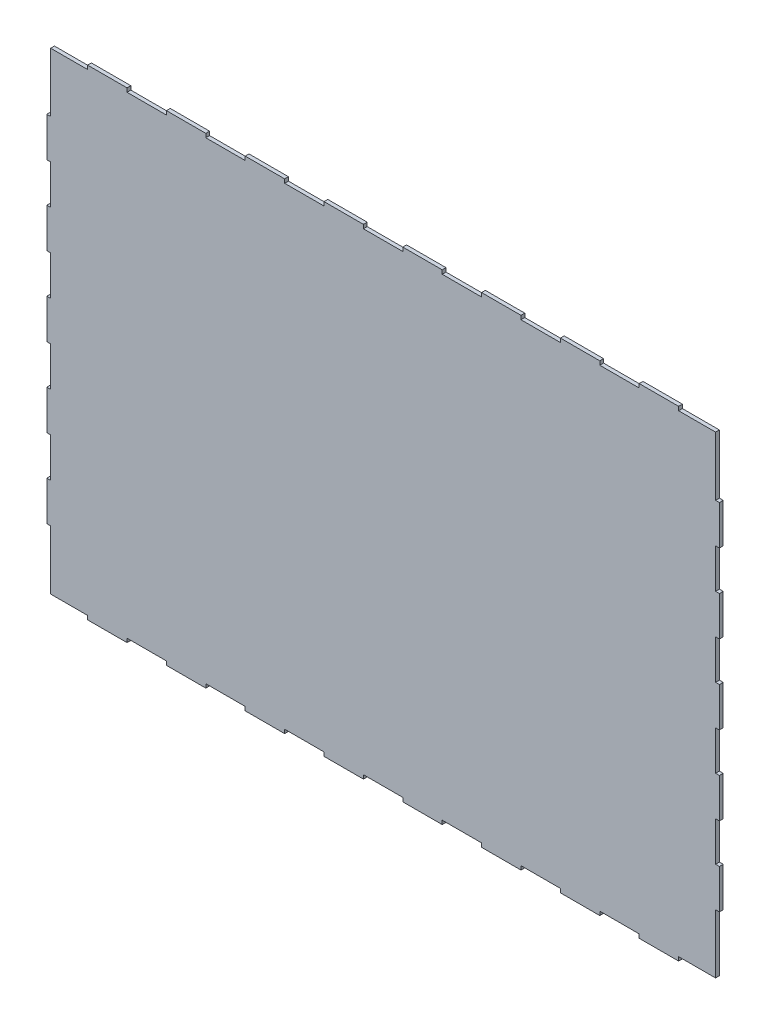
SolidWorks part; units mm, degrees
ref_plane "Front Plane" through (0, 0, 0) normal (0, 0, 1) x (1, 0, 0)
ref_plane "Top Plane" through (0, 0, 0) normal (0, 1, 0) x (1, 0, 0)
ref_plane "Right Plane" through (0, 0, 0) normal (1, 0, 0) x (0, 0, -1)
sketch "Sketch1" plane through (0, 0, 0) normal (0, 0, 1) x (1, 0, 0)
  line B0 (-1.4841, 0.1451) -> (487.4659, 0.1451)
  line B1 (487.4659, 0.1451) -> (487.4659, -50.6549)
  line B2 (487.4659, -50.6549) -> (1008.1659, -50.6549)
  line B3 (1008.1659, -50.6549) -> (1008.1659, 0.1451)
  line B4 (1008.1659, 0.1451) -> (1528.8659, 0.1451)
  line B5 (1528.8659, 0.1451) -> (1528.8659, -50.6549)
  line B6 (1528.8659, -50.6549) -> (2049.5659, -50.6549)
  line B7 (2049.5659, -50.6549) -> (2049.5659, 0.1451)
  line B8 (2049.5659, 0.1451) -> (2570.2659, 0.1451)
  line B9 (2570.2659, 0.1451) -> (2570.2659, -50.6549)
  line B10 (2570.2659, -50.6549) -> (3090.9659, -50.6549)
  line B11 (3090.9659, -50.6549) -> (3090.9659, 0.1451)
  line B12 (3090.9659, 0.1451) -> (3611.6659, 0.1451)
  line B13 (3611.6659, 0.1451) -> (3611.6659, -50.6549)
  line B14 (3611.6659, -50.6549) -> (4132.3659, -50.6549)
  line B15 (4132.3659, -50.6549) -> (4132.3659, 0.1451)
  line B16 (4132.3659, 0.1451) -> (4653.0659, 0.1451)
  line B17 (4653.0659, 0.1451) -> (4653.0659, -50.6549)
  line B18 (4653.0659, -50.6549) -> (5173.7659, -50.6549)
  line B19 (5173.7659, -50.6549) -> (5173.7659, 0.1451)
  line B20 (5173.7659, 0.1451) -> (5694.4659, 0.1451)
  line B21 (5694.4659, 0.1451) -> (5694.4659, -50.6549)
  line B22 (5694.4659, -50.6549) -> (6215.1659, -50.6549)
  line B23 (6215.1659, -50.6549) -> (6215.1659, 0.1451)
  line B24 (6215.1659, 0.1451) -> (6735.8659, 0.1451)
  line B25 (6735.8659, 0.1451) -> (6735.8659, -50.6549)
  line B26 (6735.8659, -50.6549) -> (7256.5659, -50.6549)
  line B27 (7256.5659, -50.6549) -> (7256.5659, 0.1451)
  line B28 (7256.5659, 0.1451) -> (7777.2659, 0.1451)
  line B29 (7777.2659, 0.1451) -> (7777.2659, -50.6549)
  line B30 (7777.2659, -50.6549) -> (8297.9659, -50.6549)
  line B31 (8297.9659, -50.6549) -> (8297.9659, 0.1451)
  line B32 (8297.9659, 0.1451) -> (8786.9159, 0.1451)
  line B33 (8786.9159, 0.1451) -> (8786.9159, 781.1951)
  line B34 (8786.9159, 781.1951) -> (8837.7159, 781.1951)
  line B35 (8837.7159, 781.1951) -> (8837.7159, 1301.8951)
  line B36 (8837.7159, 1301.8951) -> (8786.9159, 1301.8951)
  line B37 (8786.9159, 1301.8951) -> (8786.9159, 1822.5951)
  line B38 (8786.9159, 1822.5951) -> (8837.7159, 1822.5951)
  line B39 (8837.7159, 1822.5951) -> (8837.7159, 2343.2951)
  line B40 (8837.7159, 2343.2951) -> (8786.9159, 2343.2951)
  line B41 (8786.9159, 2343.2951) -> (8786.9159, 2863.9951)
  line B42 (8786.9159, 2863.9951) -> (8837.7159, 2863.9951)
  line B43 (8837.7159, 2863.9951) -> (8837.7159, 3384.6951)
  line B44 (8837.7159, 3384.6951) -> (8786.9159, 3384.6951)
  line B45 (8786.9159, 3384.6951) -> (8786.9159, 3905.3951)
  line B46 (8786.9159, 3905.3951) -> (8837.7159, 3905.3951)
  line B47 (8837.7159, 3905.3951) -> (8837.7159, 4426.0951)
  line B48 (8837.7159, 4426.0951) -> (8786.9159, 4426.0951)
  line B49 (8786.9159, 4426.0951) -> (8786.9159, 4946.7951)
  line B50 (8786.9159, 4946.7951) -> (8837.7159, 4946.7951)
  line B51 (8837.7159, 4946.7951) -> (8837.7159, 5467.4951)
  line B52 (8837.7159, 5467.4951) -> (8786.9159, 5467.4951)
  line B53 (8786.9159, 5467.4951) -> (8786.9159, 5988.1951)
  line B54 (8786.9159, 5988.1951) -> (8786.9159, 6248.5451)
  line B55 (8786.9159, 6248.5451) -> (8297.9659, 6248.5451)
  line B56 (8297.9659, 6248.5451) -> (8297.9659, 6299.3451)
  line B57 (8297.9659, 6299.3451) -> (7777.2659, 6299.3451)
  line B58 (7777.2659, 6299.3451) -> (7777.2659, 6248.5451)
  line B59 (7777.2659, 6248.5451) -> (7256.5659, 6248.5451)
  line B60 (7256.5659, 6248.5451) -> (7256.5659, 6299.3451)
  line B61 (7256.5659, 6299.3451) -> (6735.8659, 6299.3451)
  line B62 (6735.8659, 6299.3451) -> (6735.8659, 6248.5451)
  line B63 (6735.8659, 6248.5451) -> (6215.1659, 6248.5451)
  line B64 (6215.1659, 6248.5451) -> (6215.1659, 6299.3451)
  line B65 (6215.1659, 6299.3451) -> (5694.4659, 6299.3451)
  line B66 (5694.4659, 6299.3451) -> (5694.4659, 6248.5451)
  line B67 (5694.4659, 6248.5451) -> (5173.7659, 6248.5451)
  line B68 (5173.7659, 6248.5451) -> (5173.7659, 6299.3451)
  line B69 (5173.7659, 6299.3451) -> (4653.0659, 6299.3451)
  line B70 (4653.0659, 6299.3451) -> (4653.0659, 6248.5451)
  line B71 (4653.0659, 6248.5451) -> (4132.3659, 6248.5451)
  line B72 (4132.3659, 6248.5451) -> (4132.3659, 6299.3451)
  line B73 (4132.3659, 6299.3451) -> (3611.6659, 6299.3451)
  line B74 (3611.6659, 6299.3451) -> (3611.6659, 6248.5451)
  line B75 (3611.6659, 6248.5451) -> (3090.9659, 6248.5451)
  line B76 (3090.9659, 6248.5451) -> (3090.9659, 6299.3451)
  line B77 (3090.9659, 6299.3451) -> (2570.2659, 6299.3451)
  line B78 (2570.2659, 6299.3451) -> (2570.2659, 6248.5451)
  line B79 (2570.2659, 6248.5451) -> (2049.5659, 6248.5451)
  line B80 (2049.5659, 6248.5451) -> (2049.5659, 6299.3451)
  line B81 (2049.5659, 6299.3451) -> (1528.8659, 6299.3451)
  line B82 (1528.8659, 6299.3451) -> (1528.8659, 6248.5451)
  line B83 (1528.8659, 6248.5451) -> (1008.1659, 6248.5451)
  line B84 (1008.1659, 6248.5451) -> (1008.1659, 6299.3451)
  line B85 (1008.1659, 6299.3451) -> (487.4659, 6299.3451)
  line B86 (487.4659, 6299.3451) -> (487.4659, 6248.5451)
  line B87 (487.4659, 6248.5451) -> (-1.4841, 6248.5451)
  line B88 (-1.4841, 6248.5451) -> (-1.4841, 5467.4951)
  line B89 (-1.4841, 5467.4951) -> (-52.2841, 5467.4951)
  line B90 (-52.2841, 5467.4951) -> (-52.2841, 4946.7951)
  line B91 (-52.2841, 4946.7951) -> (-1.4841, 4946.7951)
  line B92 (-1.4841, 4946.7951) -> (-1.4841, 4426.0951)
  line B93 (-1.4841, 4426.0951) -> (-52.2841, 4426.0951)
  line B94 (-52.2841, 4426.0951) -> (-52.2841, 3905.3951)
  line B95 (-52.2841, 3905.3951) -> (-1.4841, 3905.3951)
  line B96 (-1.4841, 3905.3951) -> (-1.4841, 3384.6951)
  line B97 (-1.4841, 3384.6951) -> (-52.2841, 3384.6951)
  line B98 (-52.2841, 3384.6951) -> (-52.2841, 2863.9951)
  line B99 (-52.2841, 2863.9951) -> (-1.4841, 2863.9951)
  line B100 (-1.4841, 2863.9951) -> (-1.4841, 2343.2951)
  line B101 (-1.4841, 2343.2951) -> (-52.2841, 2343.2951)
  line B102 (-52.2841, 2343.2951) -> (-52.2841, 1822.5951)
  line B103 (-52.2841, 1822.5951) -> (-1.4841, 1822.5951)
  line B104 (-1.4841, 1822.5951) -> (-1.4841, 1301.8951)
  line B105 (-1.4841, 1301.8951) -> (-52.2841, 1301.8951)
  line B106 (-52.2841, 1301.8951) -> (-52.2841, 781.1951)
  line B107 (-52.2841, 781.1951) -> (-1.4841, 781.1951)
  line B108 (-1.4841, 781.1951) -> (-1.4841, 260.4951)
  line B109 (-1.4841, 260.4951) -> (-1.4841, 0.1451)
sketch_block_instance "back-1"
sketch_block "back"
extrude "Boss-Extrude1" add sketch "Sketch1" along normal blind 50
scale "Scale1" scale about centroid uniform scaling yes scale factor 0.04
